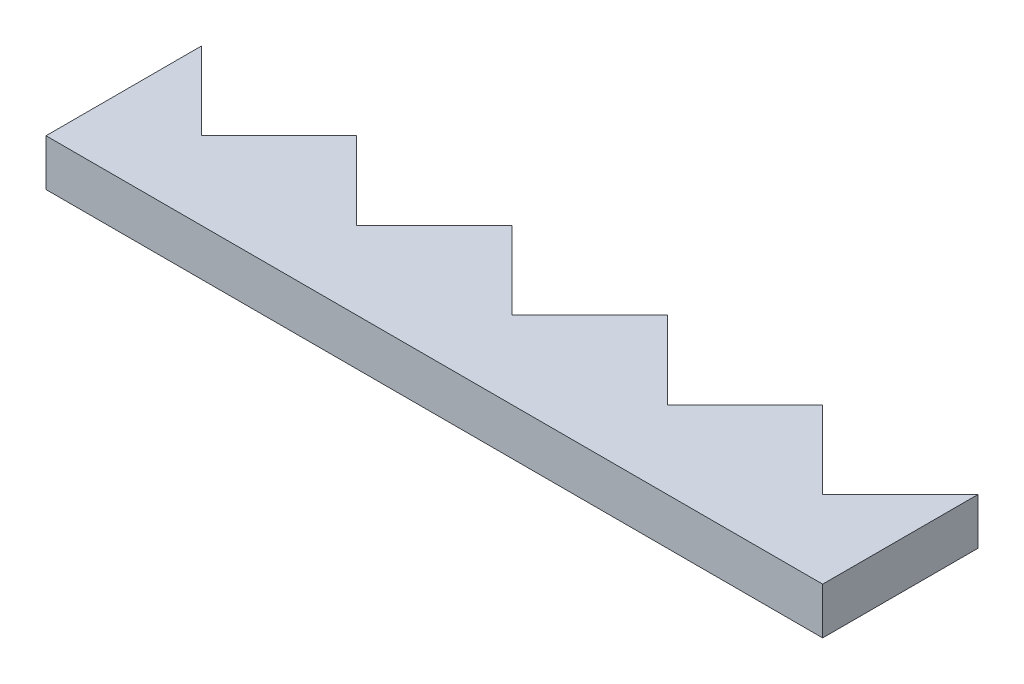
SolidWorks part; units mm, degrees
ref_plane "Front Plane" through (0, 0, 0) normal (0, 0, 1) x (1, 0, 0)
ref_plane "Top Plane" through (0, 0, 0) normal (0, 1, 0) x (1, 0, 0)
ref_plane "Right Plane" through (0, 0, 0) normal (1, 0, 0) x (0, 0, -1)
sketch "Sketch1" plane through (0, 0.3303, 0) normal (0, 1, 0) x (1, 0, 0)
  line L0 (0, 0) -> (0, 10)
  line L1 (0, 10) -> (5, 5)
  line L2 (5, 5) -> (10, 10)
  line L4 (10, 10) -> (15, 5)
  line L5 (15, 5) -> (20, 10)
  line L6 (20, 10) -> (25, 5)
  line L7 (25, 5) -> (30, 10)
  line L8 (30, 10) -> (35, 5)
  line L9 (35, 5) -> (40, 10)
  line L10 (40, 10) -> (45, 5)
  line L11 (45, 5) -> (50, 10)
  line L16 (0, 0) -> (50, 0)
  line L17 (50, 0) -> (50, 10)
  point P3 (51.1505, 10)
  point P6 (51.2091, 10)
  point P8 (50, 10)
  point P11 (0, 0)
  dimension "D1" = 10
  dimension "D2" = 10
  dimension "D3" = 5
  dimension "D4" = 5
extrude "Boss-Extrude1" add sketch "Sketch1" along normal blind 3
